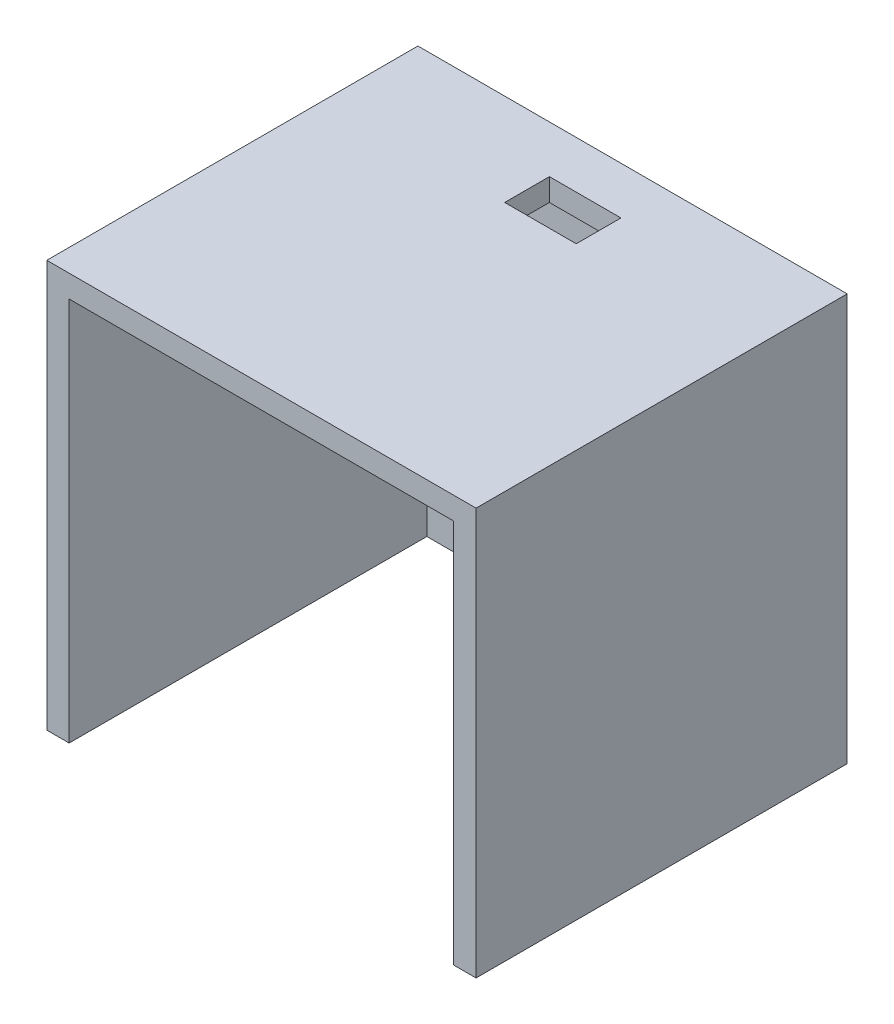
SolidWorks part; units mm, degrees
material "Alliage 1060"
ref_plane "Plan de dessus" through (0, 0, 0) normal (0, 0, 1) x (1, 0, 0)
ref_plane "Plan de droite" through (0, 0, 0) normal (0, 1, 0) x (1, 0, 0)
ref_plane "Plan de face" through (0, 0, 0) normal (1, 0, 0) x (0, 0, -1)
sketch "Esquisse1" plane through (0, 0, 0) normal (0, 0, 1) x (1, 0, 0)
  line L0 (43, 43) -> (0, 0) construction
  line L1 (0, 0) -> (43, 0)
  line L2 (0, 0) -> (0, 43)
  line L3 (0, 43) -> (43, 43)
  line L4 (43, 0) -> (43, 43)
  line L9 (45.5, -2.5) -> (21.5, 21.5) construction
  line L21 (-2.5, 43) -> (-2.5, -2.5)
  line L22 (-2.5, 43) -> (-2.5, 45.5)
  line L23 (-2.5, 45.5) -> (45.5, 45.5)
  line L25 (45.5, 43) -> (45.5, 45.5)
  line L26 (45.5, 43) -> (45.5, -2.5)
  line L28 (0, -2.5) -> (45.5, -2.5)
  line L29 (0, -2.5) -> (-2.5, -2.5)
  point P5 (-2.5, 43)
  point P7 (0, 0)
  dimension "D1" = 43
  dimension "D2" = 43
extrude "Boss.-Extru.1" add sketch "Esquisse1" along normal blind 40
sketch "Esquisse2" plane through (0, 0, 0) normal (0, 0, 1) x (1, 0, 0)
  line L5 (-2.5, 45.5) -> (45.5, 45.5)
  line L6 (-2.5, 45.5) -> (-2.5, -2.5)
  line L7 (-2.5, -2.5) -> (45.5, -2.5)
  line L8 (45.5, 45.5) -> (45.5, -2.5)
extrude "Boss.-Extru.2" add sketch "Esquisse2" against normal blind 1.5
sketch "Esquisse5" plane through (0, 45.5, 0) normal (0, 1, 0) x (1, 0, 0)
  line L0 (17.5, -3.8) -> (25.5, -3.8)
  line L1 (25.5, -8.8) -> (17.5, -8.8)
  line L2 (25.5, -3.8) -> (25.5, -8.8)
  line L3 (17.5, -3.8) -> (17.5, -8.8)
  line L4 (45.5, -40) -> (45.5, 1.5) construction
  line L5 (-2.5, -19.25) -> (45.5, -19.25) construction
  line L6 (-2.5, -40) -> (-2.5, 1.5) construction
  line L7 (21.5, 1.5) -> (21.5, -40) construction
  line L8 (45.5, 1.5) -> (-2.5, 1.5) construction
  line L9 (45.5, -40) -> (-2.5, -40) construction
  point P5 (21.5, -8.8)
  point P17 (21.5, -3.8)
  dimension "D1" = 4
  dimension "D2" = 5.3
extrude "Enlèv. mat.-Extru.3" cut sketch "Esquisse5" against normal up to next
sketch "Esquisse6" plane through (0, 0, 40) normal (0, 0, 1) x (1, 0, 0)
  line L1 (-4.2276, 0) -> (50.5536, 0)
  line L2 (-4.2276, 0) -> (-4.2276, -3.0788)
  line L3 (-4.2276, -3.0788) -> (50.5536, -3.0788)
  line L4 (50.5536, 0) -> (50.5536, -3.0788)
extrude "Enlèv. mat.-Extru.4" cut sketch "Esquisse6" against normal up to next
